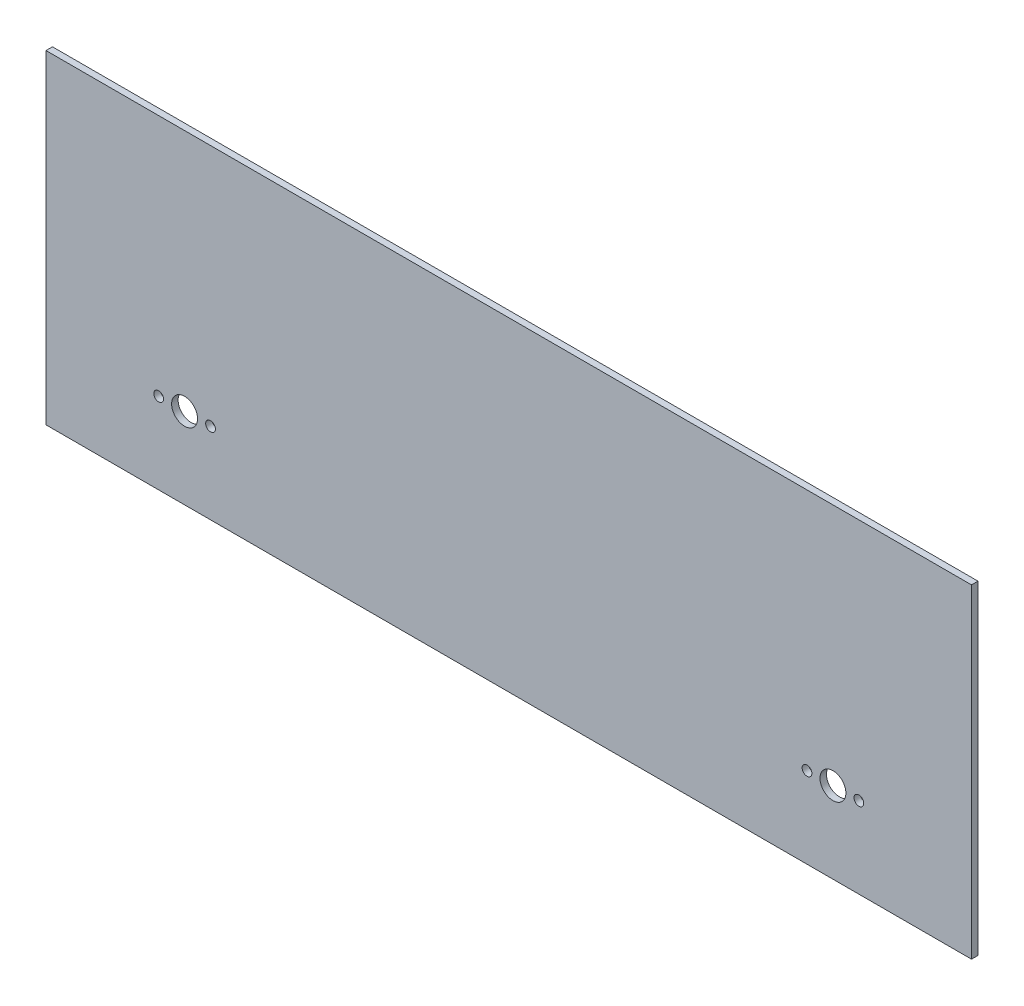
SolidWorks part; units mm, degrees
ref_plane "Front Plane" through (0, 0, 0) normal (0, 0, 1) x (1, 0, 0)
ref_plane "Top Plane" through (0, 0, 0) normal (0, 1, 0) x (1, 0, 0)
ref_plane "Right Plane" through (0, 0, 0) normal (1, 0, 0) x (0, 0, -1)
sketch "Sketch1" plane through (0, 0, 0) normal (0, 0, 1) x (1, 0, 0)
  line L0 (0, 32.322) -> (0, -34.4767) construction
  line L1 (-142.75, 50) -> (142.75, 50)
  line L2 (-142.75, 50) -> (-142.75, -50)
  line L3 (-142.75, -50) -> (142.75, -50)
  line L4 (142.75, 50) -> (142.75, -50)
  line L5 (-142.75, 50) -> (142.75, -50) construction
  line L6 (-142.75, -50) -> (142.75, 50) construction
  circle A0 centre (-100, -25) radius 4
  circle A1 centre (-92, -25) radius 1.5
  circle A2 centre (-108, -25) radius 1.5
  circle A3 centre (108, -25) radius 1.5
  circle A4 centre (92, -25) radius 1.5
  circle A5 centre (100, -25) radius 4
  point P0 (0, 0)
  dimension "D5" = 8
  dimension "D6" = 3
  dimension "D1" = 285.5
  dimension "D2" = 100
  dimension "D3" = 25
  dimension "D4" = 42.75
  dimension "D7" = 8
  dimension "D8" = 8
extrude "Boss-Extrude1" add sketch "Sketch1" along normal blind 2
